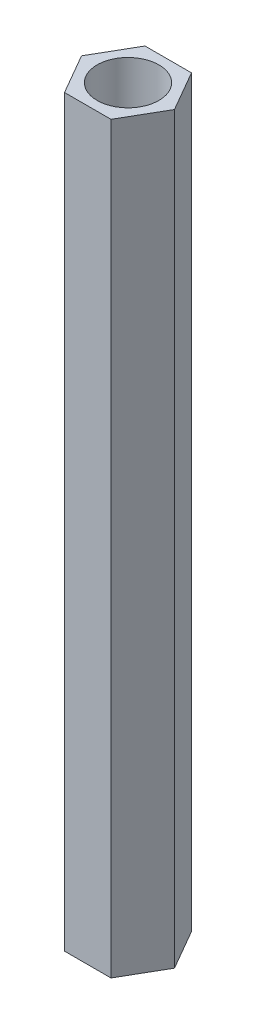
SolidWorks part; units mm, degrees
ref_plane "Front Plane" through (0, 0, 0) normal (0, 0, 1) x (1, 0, 0)
ref_plane "Top Plane" through (0, 0, 0) normal (0, 1, 0) x (1, 0, 0)
ref_plane "Right Plane" through (0, 0, 0) normal (1, 0, 0) x (0, 0, -1)
sketch "Sketch1" plane through (0, 0, 0) normal (0, 1, 0) x (1, 0, 0)
  line L1 (2.5, 0) -> (1.25, 2.1651)
  line L2 (1.25, 2.1651) -> (-1.25, 2.1651)
  line L3 (-1.25, 2.1651) -> (-2.5, 0)
  line L4 (-2.5, 0) -> (-1.25, -2.1651)
  line L5 (-1.25, -2.1651) -> (1.25, -2.1651)
  line L6 (1.25, -2.1651) -> (2.5, 0)
  circle A0 centre (0, 0) radius 2.1651 construction
  dimension "D1" = 2.5
extrude "Boss-Extrude1" add sketch "Sketch1" along normal blind 40
sketch "Sketch2" plane through (0, 40, 0) normal (0, 1, 0) x (1, 0, 0)
  circle A0 centre (0, 0) radius 1.6604
extrude "Cut-Extrude1" cut sketch "Sketch2" against normal through all
